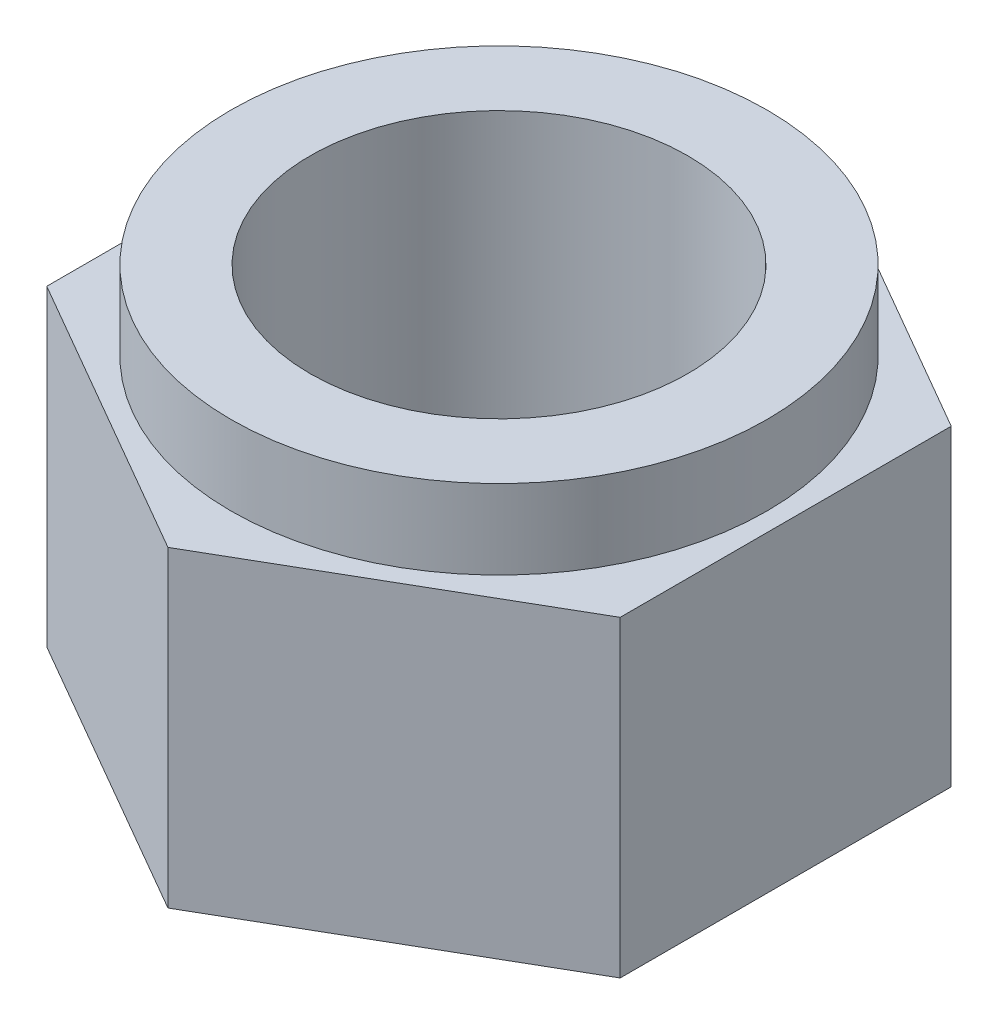
SolidWorks part; units mm, degrees
ref_plane "Front Plane" through (0, 0, 0) normal (0, 0, 1) x (1, 0, 0)
ref_plane "Top Plane" through (0, 0, 0) normal (0, 1, 0) x (1, 0, 0)
ref_plane "Right Plane" through (0, 0, 0) normal (1, 0, 0) x (0, 0, -1)
sketch "Sketch1" plane through (0, 0, 0) normal (0, 1, 0) x (1, 0, 0)
  line L1 (3.1674, -0.5285) -> (3.1674, 6.5729)
  line L2 (3.1674, 6.5729) -> (-2.9826, 10.1236)
  line L3 (-2.9826, 10.1236) -> (-9.1326, 6.5729)
  line L4 (-9.1326, 6.5729) -> (-9.1326, -0.5285)
  line L5 (-9.1326, -0.5285) -> (-2.9826, -4.0792)
  line L6 (-2.9826, -4.0792) -> (3.1674, -0.5285)
  circle A0 centre (-2.9826, 3.0222) radius 6.15 construction
  circle A1 centre (-2.9826, 3.0222) radius 4.05
  dimension "D2" = 8.1
  dimension "D1" = 12.3
extrude "Boss-Extrude1" add sketch "Sketch1" along normal blind 6.7
sketch "Sketch2" plane through (0, 6.7, 0) normal (0, 1, 0) x (1, 0, 0)
  circle A0 centre (-2.9826, 3.0222) radius 4.05
  circle A2 centre (-2.9826, 3.0222) radius 5.75
  dimension "D1" = 1.7
extrude "Boss-Extrude2" add sketch "Sketch2" along normal blind 1.7
